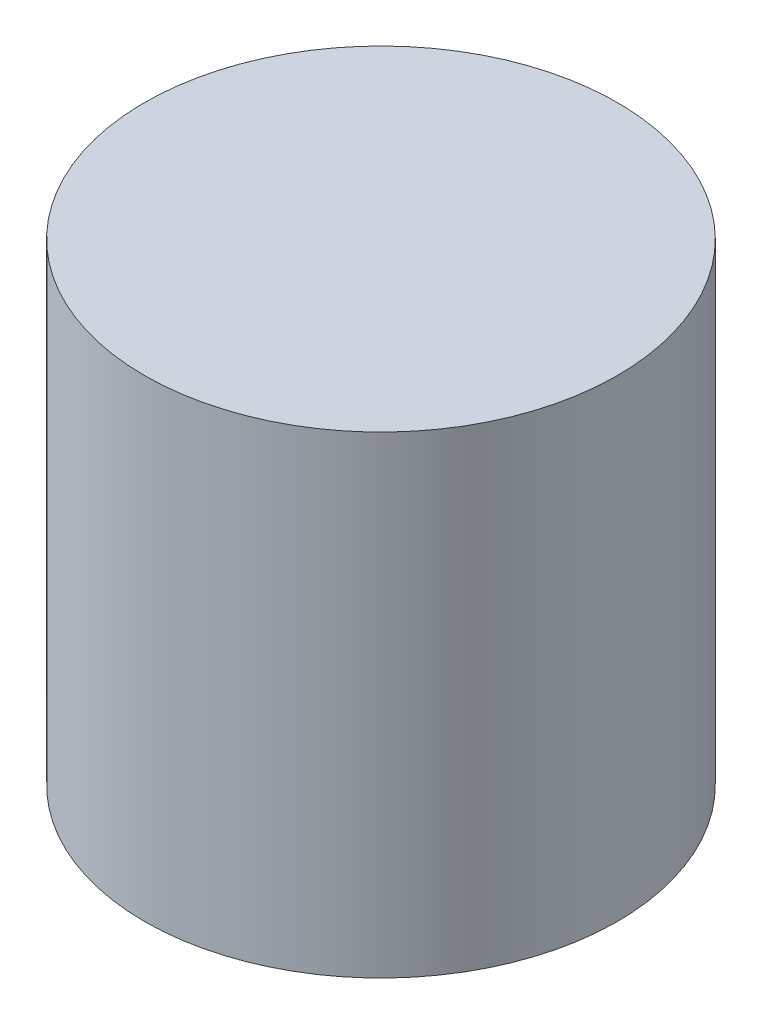
SolidWorks part; units mm, degrees
material "Nickel"
ref_plane "Front Plane" through (0, 0, 0) normal (0, 0, 1) x (1, 0, 0)
ref_plane "Top Plane" through (0, 0, 0) normal (0, 1, 0) x (1, 0, 0)
ref_plane "Right Plane" through (0, 0, 0) normal (1, 0, 0) x (0, 0, -1)
sketch "Sketch1" plane through (0, 0, 0) normal (0, 1, 0) x (1, 0, 0)
  circle A0 centre (0, 0) radius 6.35
  dimension "D1" = 12.7
extrude "Boss-Extrude1" add sketch "Sketch1" along normal blind 12.7
